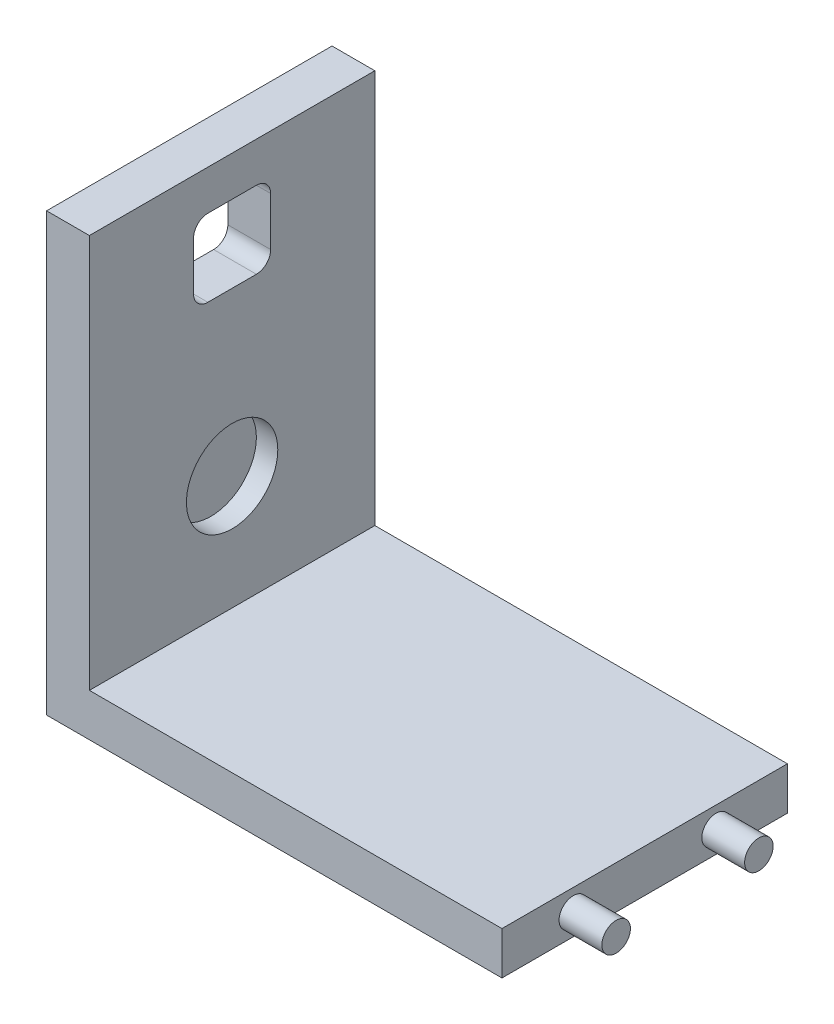
SolidWorks part; units mm, degrees
ref_plane "Ön Düzlem" through (0, 0, 0) normal (0, 0, 1) x (1, 0, 0)
ref_plane "Üst Düzlem" through (0, 0, 0) normal (0, 1, 0) x (1, 0, 0)
ref_plane "Sağ Düzlem" through (0, 0, 0) normal (1, 0, 0) x (0, 0, -1)
sketch "Çizim1" plane through (0, 0, 0) normal (0, 0, 1) x (1, 0, 0)
  line L0 (-87.2699, 0) -> (72.2699, 0)
  line L1 (-87.2699, 0) -> (-87.2699, 153)
  line L3 (72.2699, 0) -> (72.2699, 15)
  line L4 (-87.2699, 153) -> (-72.2699, 153)
  line L5 (-72.2699, 153) -> (-72.2699, 15)
  line L6 (72.2699, 15) -> (-72.2699, 15)
  point P4 (0, 0)
extrude "Yükseklik-Ekstrüzyon1" add sketch "Çizim1" against normal blind 100
ref_plane "Düzlem1" through (-72.2699, 0, 0) normal (1, 0, 0) x (0, 0, -1)
sketch "Çizim2" plane through (-72.2699, 0, 0) normal (1, 0, 0) x (0, 0, -1)
  circle A0 centre (50, 55) radius 16
sketch "Çizim3" plane through (-72.2699, 0, 0) normal (1, 0, 0) x (0, 0, -1)
  line L1 (41.5, 139) -> (58.5, 139)
  line L2 (36.5, 134) -> (36.5, 117)
  line L3 (41.5, 112) -> (58.5, 112)
  line L4 (63.5, 134) -> (63.5, 117)
  line L5 (36.5, 139) -> (63.5, 112) construction
  line L6 (36.5, 112) -> (63.5, 139) construction
  arc A1 (58.5, 112) -> (63.5, 117) centre (58.5, 117) ccw
  arc A2 (36.5, 117) -> (41.5, 112) centre (41.5, 117) ccw
  arc A3 (58.5, 139) -> (63.5, 134) centre (58.5, 134) cw
  arc A4 (41.5, 139) -> (36.5, 134) centre (41.5, 134) ccw
  dimension "D1" = 5
ref_plane "Düzlem2" through (72.2699, 0, 0) normal (1, 0, 0) x (0, 0, -1)
sketch "Çizim4" plane through (72.2699, 0, 0) normal (1, 0, 0) x (0, 0, -1)
  circle A0 centre (25, 7.5) radius 5
  circle A1 centre (75, 7.5) radius 5
extrude "Yükseklik-Ekstrüzyon2" add sketch "Çizim4" along normal blind 15
extrude "Kes-Ekstrüzyon7" cut sketch "Çizim2" against normal blind 7.5
extrude "Kes-Ekstrüzyon8" cut sketch "Çizim3" against normal through all
